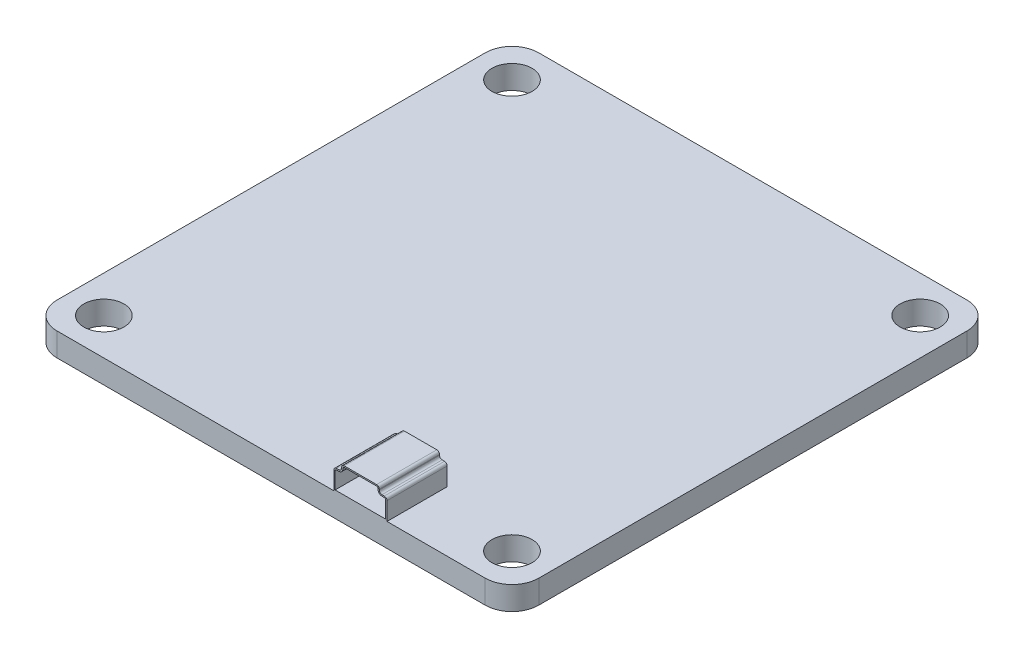
SolidWorks part; units mm, degrees
ref_plane "Front Plane" through (0, 0, 0) normal (0, 0, 1) x (1, 0, 0)
ref_plane "Top Plane" through (0, 0, 0) normal (0, 1, 0) x (1, 0, 0)
ref_plane "Right Plane" through (0, 0, 0) normal (1, 0, 0) x (0, 0, -1)
sketch "Sketch1" plane through (0, 0, 0) normal (0, 1, 0) x (1, 0, 0)
  line L1 (-16, -18) -> (16, -18)
  line L2 (-18, -16) -> (-18, 16)
  line L3 (-16, 18) -> (16, 18)
  line L4 (18, -16) -> (18, 16)
  line L5 (-18, -18) -> (18, 18) construction
  line L6 (-18, 18) -> (18, -18) construction
  line L7 (-15.25, -15.25) -> (15.25, -15.25) construction
  line L8 (-15.25, -15.25) -> (-15.25, 15.25) construction
  line L9 (-15.25, 15.25) -> (15.25, 15.25) construction
  line L10 (15.25, -15.25) -> (15.25, 15.25) construction
  line L11 (-15.25, -15.25) -> (15.25, 15.25) construction
  line L12 (-15.25, 15.25) -> (15.25, -15.25) construction
  circle A0 centre (-15.25, 15.25) radius 1.5
  circle A1 centre (15.25, 15.25) radius 1.5
  circle A2 centre (-15.25, -15.25) radius 1.5
  circle A3 centre (15.25, -15.25) radius 1.5
  arc A5 (-16, -18) -> (-18, -16) centre (-16, -16) cw
  arc A6 (16, -18) -> (18, -16) centre (16, -16) ccw
  arc A7 (16, 18) -> (18, 16) centre (16, 16) cw
  arc A8 (-18, 16) -> (-16, 18) centre (-16, 16) cw
  point P0 (0, 0)
  point P6 (0, 0)
  dimension "D3" = 2
  dimension "D1" = 36
  dimension "D2" = 30.5
extrude "Boss-Extrude1" add sketch "Sketch1" along normal blind 1.75
sketch "Sketch2" plane through (0, 0, 18) normal (0, 0, 1) x (1, 0, 0)
  line L0 (-16, 1.75) -> (16, 1.75) construction
  line L1 (4.6831, 1.75) -> (8.66, 1.75)
  line L2 (4.6831, 1.75) -> (4.6831, 3.094)
  line L3 (5.4615, 3.75) -> (7.8815, 3.75)
  line L4 (8.66, 1.75) -> (8.66, 3.094)
  line L5 (4.8831, 3.294) -> (5.0615, 3.294)
  line L6 (5.2615, 3.494) -> (5.2615, 3.55)
  line L7 (8.46, 3.294) -> (8.2815, 3.294)
  line L8 (8.0815, 3.494) -> (8.0815, 3.55)
  line L9 (4.7831, 1.85) -> (4.7831, 3.094)
  line L10 (4.8831, 3.194) -> (5.0615, 3.194)
  line L11 (5.3615, 3.494) -> (5.3615, 3.55)
  line L12 (5.4615, 3.65) -> (7.8815, 3.65)
  line L13 (7.9815, 3.494) -> (7.9815, 3.55)
  line L14 (8.46, 3.194) -> (8.2815, 3.194)
  line L15 (8.56, 1.85) -> (8.56, 3.094)
  line L16 (4.7831, 1.85) -> (8.56, 1.85)
  arc A0 (8.46, 3.294) -> (8.66, 3.094) centre (8.46, 3.094) cw
  arc A1 (8.2815, 3.294) -> (8.0815, 3.494) centre (8.2815, 3.494) cw
  arc A2 (8.0815, 3.55) -> (7.8815, 3.75) centre (7.8815, 3.55) ccw
  arc A3 (5.2615, 3.55) -> (5.4615, 3.75) centre (5.4615, 3.55) cw
  arc A4 (5.0615, 3.294) -> (5.2615, 3.494) centre (5.0615, 3.494) ccw
  arc A5 (4.8831, 3.294) -> (4.6831, 3.094) centre (4.8831, 3.094) ccw
  arc A6 (4.8831, 3.194) -> (4.7831, 3.094) centre (4.8831, 3.094) ccw
  arc A7 (5.0615, 3.194) -> (5.3615, 3.494) centre (5.0615, 3.494) ccw
  arc A8 (5.3615, 3.55) -> (5.4615, 3.65) centre (5.4615, 3.55) cw
  arc A9 (7.9815, 3.55) -> (7.8815, 3.65) centre (7.8815, 3.55) ccw
  arc A10 (8.2815, 3.194) -> (7.9815, 3.494) centre (8.2815, 3.494) cw
  arc A11 (8.46, 3.194) -> (8.56, 3.094) centre (8.46, 3.094) cw
  point P20 (5.2615, 3.294)
  dimension "D1" = 0.2
  dimension "D2" = 0.1
extrude "Boss-" add sketch "Sketch2" against normal blind 3 contours A1 L8 A2 L3 A3 L6 A4 L5 A5 L2 L1 L4 A0 L7 | L15 A11 L14 A10 L13 A9 L12 A8 L11 A7 L10 A6 L9 L16
sketch "Sketch9" plane through (0, 0, 15) normal (0, 0, -1) x (-1, 0, 0)
  line L8 (-8.2815, 3.294) -> (-8.46, 3.294)
  line L9 (-8.66, 3.094) -> (-8.66, 1.75)
  line L10 (-8.66, 1.75) -> (-4.6831, 1.75)
  line L11 (-4.6831, 1.75) -> (-4.6831, 3.094)
  line L12 (-4.8831, 3.294) -> (-5.0615, 3.294)
  line L13 (-5.2615, 3.494) -> (-5.2615, 3.55)
  line L14 (-5.4615, 3.75) -> (-7.8815, 3.75)
  line L15 (-8.0815, 3.55) -> (-8.0815, 3.494)
  line L16 (-8.2815, 3.294) -> (-8.46, 3.294)
  line L17 (-8.66, 3.094) -> (-8.66, 1.75)
  line L18 (-8.66, 1.75) -> (-4.6831, 1.75)
  line L19 (-4.6831, 1.75) -> (-4.6831, 3.094)
  line L20 (-4.8831, 3.294) -> (-5.0615, 3.294)
  line L21 (-5.2615, 3.494) -> (-5.2615, 3.55)
  line L22 (-5.4615, 3.75) -> (-7.8815, 3.75)
  line L23 (-8.0815, 3.55) -> (-8.0815, 3.494)
  arc A6 (-8.46, 3.294) -> (-8.66, 3.094) centre (-8.46, 3.094) ccw
  arc A7 (-4.6831, 3.094) -> (-4.8831, 3.294) centre (-4.8831, 3.094) ccw
  arc A8 (-5.2615, 3.494) -> (-5.0615, 3.294) centre (-5.0615, 3.494) ccw
  arc A9 (-5.2615, 3.55) -> (-5.4615, 3.75) centre (-5.4615, 3.55) ccw
  arc A10 (-7.8815, 3.75) -> (-8.0815, 3.55) centre (-7.8815, 3.55) ccw
  arc A11 (-8.2815, 3.294) -> (-8.0815, 3.494) centre (-8.2815, 3.494) ccw
  arc A12 (-8.46, 3.294) -> (-8.66, 3.094) centre (-8.46, 3.094) ccw
  arc A13 (-4.6831, 3.094) -> (-4.8831, 3.294) centre (-4.8831, 3.094) ccw
  arc A14 (-5.2615, 3.494) -> (-5.0615, 3.294) centre (-5.0615, 3.494) ccw
  arc A15 (-5.2615, 3.55) -> (-5.4615, 3.75) centre (-5.4615, 3.55) ccw
  arc A16 (-7.8815, 3.75) -> (-8.0815, 3.55) centre (-7.8815, 3.55) ccw
  arc A17 (-8.2815, 3.294) -> (-8.0815, 3.494) centre (-8.2815, 3.494) ccw
  dimension "D1" = 0
extrude "Boss-Extrude5" add sketch "Sketch9" along normal blind 1.5
sketch "Sketch10" plane through (0, 0, 13.5) normal (0, 0, -1) x (-1, 0, 0)
  circle A0 centre (-6.6869, 2.5628) radius 0.25
  circle A1 centre (-5.8869, 2.5628) radius 0.25
  circle A2 centre (-7.4869, 2.5628) radius 0.25
  dimension "D3" = 0.5
  dimension "D4" = 0.5
  dimension "D5" = 0.5
  dimension "D1" = 0.8
  dimension "D2" = 0.8
extrude "Cut-Extrude2" cut sketch "Sketch10" against normal through all contours A1 | A0 | A2
